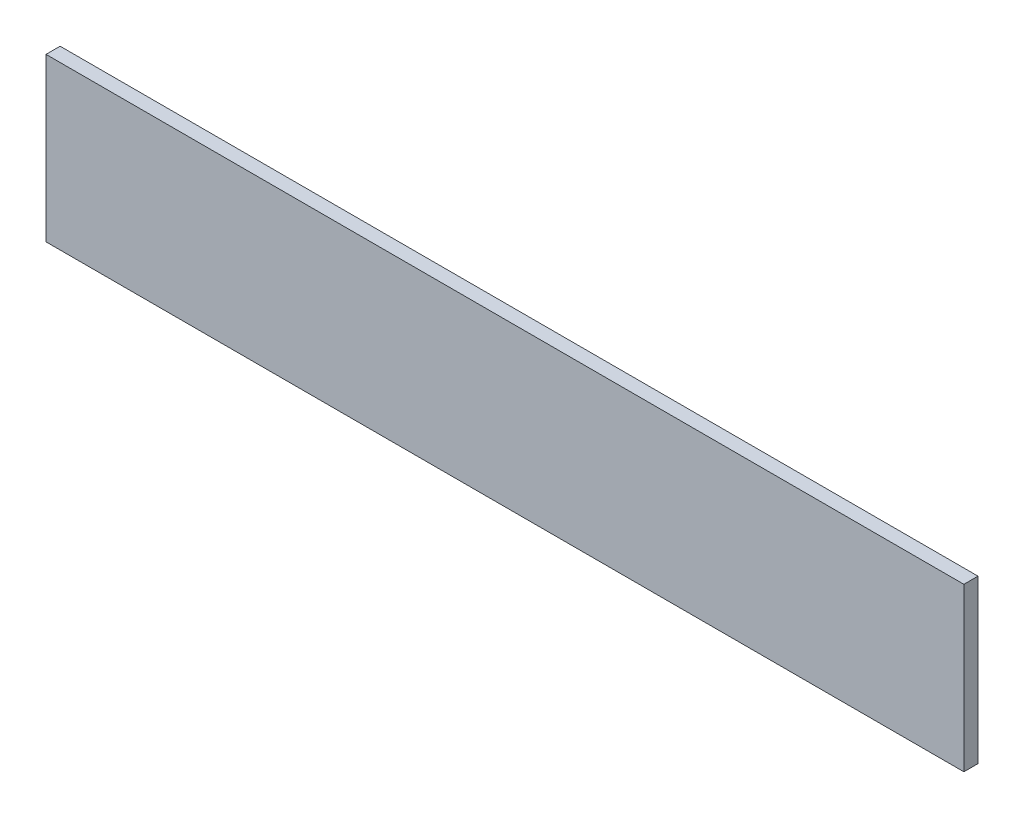
SolidWorks part; units mm, degrees
material " 09Г2С ГОСТ 4543-71"
ref_plane "Спереди" through (0, 0, 0) normal (0, 0, 1) x (1, 0, 0)
ref_plane "Сверху" through (0, 0, 0) normal (0, 1, 0) x (1, 0, 0)
ref_plane "Слева" through (0, 0, 0) normal (1, 0, 0) x (0, 0, -1)
sketch "Эскиз1" plane through (0, 0, 0) normal (0, 0, 1) x (1, 0, 0)
  line L1 (0, 0) -> (260, 0)
  line L2 (0, 0) -> (0, 46)
  line L3 (0, 46) -> (260, 46)
  line L4 (260, 0) -> (260, 46)
  dimension "D1" = 260
  dimension "D2" = 46
extrude "Вытянуть1" add sketch "Эскиз1" along normal blind 4
